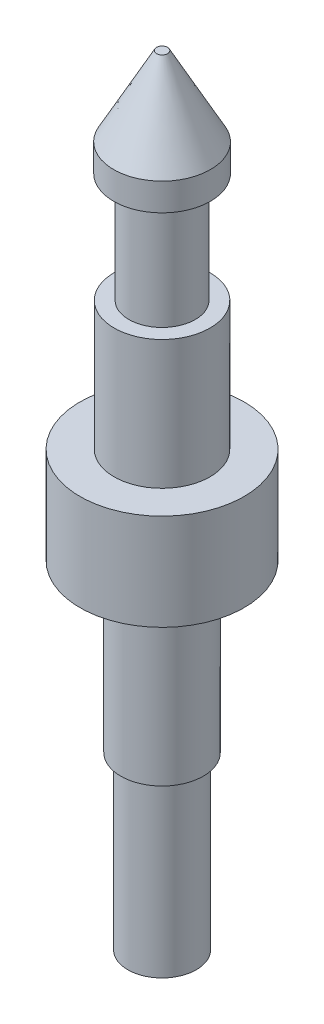
SolidWorks part; units mm, degrees
ref_plane "Front Plane" through (0, 0, 0) normal (0, 0, 1) x (1, 0, 0)
ref_plane "Top Plane" through (0, 0, 0) normal (0, 1, 0) x (1, 0, 0)
ref_plane "Right Plane" through (0, 0, 0) normal (1, 0, 0) x (0, 0, -1)
sketch "Sketch1" plane through (0, 0, 0) normal (0, 0, 1) x (1, 0, 0)
  line L0 (0, 0) -> (0, 79.052) construction
  line L1 (0, 0) -> (1.9812, 0)
  line L2 (2.3813, 9.8806) -> (2.3813, 19.4818)
  line L3 (2.3813, 19.4818) -> (4.7371, 19.4818)
  line L4 (2.7686, 25.0444) -> (2.7686, 32.4866)
  line L5 (2.7686, 32.4866) -> (1.9177, 32.4866)
  line L6 (1.9177, 32.4866) -> (1.9177, 38.8366)
  line L7 (1.9177, 38.8366) -> (2.794, 38.8366)
  line L8 (2.794, 38.8366) -> (2.794, 40.4241)
  line L9 (2.794, 40.4241) -> (0.3175, 44.9834)
  line L10 (0.3175, 44.9834) -> (0, 44.9834)
  line L11 (0, 44.9834) -> (0, 0)
  line L12 (2.3813, 9.8806) -> (1.9812, 9.8806)
  line L13 (1.9812, 9.8806) -> (1.9812, 0)
  line L14 (2.7686, 25.0444) -> (4.7371, 25.0444)
  line L15 (4.7371, 25.0444) -> (4.7371, 19.4818)
  dimension "D1" = 19.4818
  dimension "D2" = 9.8806
  dimension "D3" = 6.35
  dimension "D4" = 1.5875
  dimension "D5" = 25.5016
  dimension "D6" = 5.588
  dimension "D7" = 0.635
  dimension "D8" = 3.8354
  dimension "D9" = 5.5372
  dimension "D10" = 4.7625
  dimension "D11" = 3.9624
  dimension "D12" = 9.4742
  dimension "D13" = 5.5626
  dimension "D14" = 13.0048
revolve "Revolve1" add sketch "Sketch1" angle 360 about L0
ref_plane "Plane1" through (0, 35.6616, 0) normal (0, 1, 0) x (1, 0, 0)
sketch "Sketch3" plane through (0, 0, 0) normal (0, 0, 1) x (1, 0, 0)
  line L0 (1.9177, 32.4866) -> (1.9177, 38.8366) construction
  line L1 (1.9177, 32.4866) -> (1.9177, 38.8366)
  line L2 (1.9177, 38.8366) -> (3.4417, 38.8366)
  line L3 (1.9177, 32.4866) -> (3.4417, 32.4866)
  arc A0 (3.4417, 38.8366) -> (3.4417, 32.4866) centre (3.4417, 35.6616) cw
  dimension "D1" = 1.524
revolve "Revolve2-Mini_Post_Rubber_supress" [suppressed] add sketch "Sketch3" angle 360
sketch "Sketch4" plane through (0, 35.6616, 0) normal (0, 1, 0) x (1, 0, 0)
  circle A0 centre (0, 0) radius 4.0386 construction
  dimension "D1" = 8.0772
